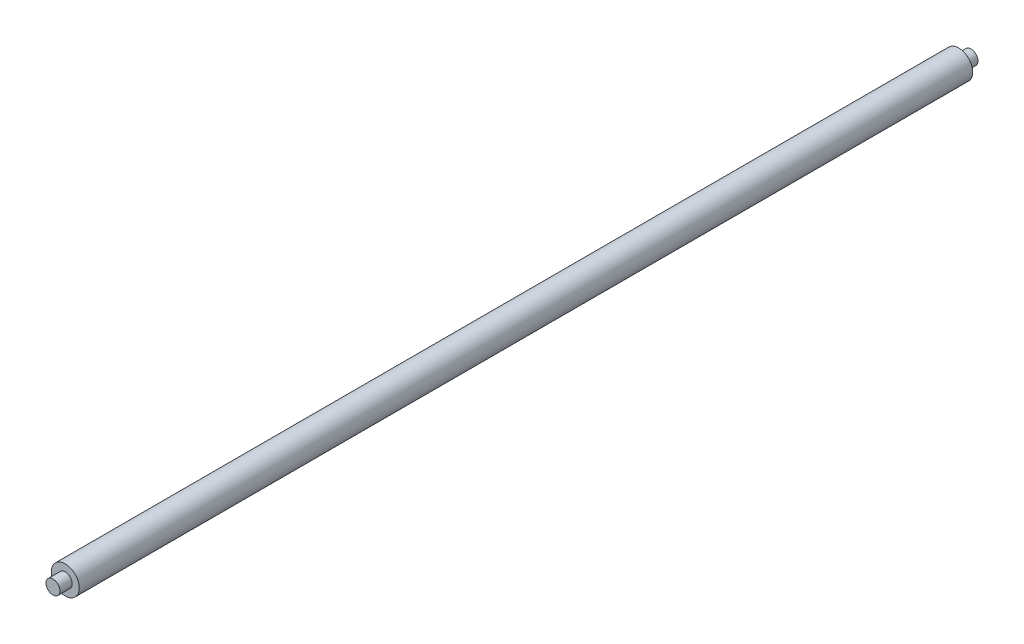
SolidWorks part; units mm, degrees
ref_plane "Front Plane" through (0, 0, 0) normal (0, 0, 1) x (1, 0, 0)
ref_plane "Top Plane" through (0, 0, 0) normal (0, 1, 0) x (1, 0, 0)
ref_plane "Right Plane" through (0, 0, 0) normal (1, 0, 0) x (0, 0, -1)
sketch "Sketch1" plane through (0, 0, 0) normal (0, 0, 1) x (1, 0, 0)
  circle A0 centre (0, 0) radius 6.25
  dimension "D1" = 12.5
extrude "Boss-Extrude1" add sketch "Sketch1" along normal blind 11
sketch "Sketch2" plane through (0, 0, 11) normal (0, 0, 1) x (1, 0, 0)
  circle A0 centre (0, 0) radius 12.5
  dimension "D1" = 25
extrude "Boss-Extrude2" add sketch "Sketch2" along normal blind 800
sketch "Sketch3" plane through (0, 0, 811) normal (0, 0, 1) x (1, 0, 0)
  circle A0 centre (0, 0) radius 6.25
  dimension "D1" = 12.5
extrude "Boss-Extrude3" add sketch "Sketch3" along normal blind 11
sketch "Sketch4" plane through (0, 0, 822) normal (0, 0, 1) x (1, 0, 0)
  circle A0 centre (0, 0) radius 4
  circle A1 centre (0, 0) radius 6.25
  circle A2 centre (0, 0) radius 6.25
  dimension "D1" = 0
